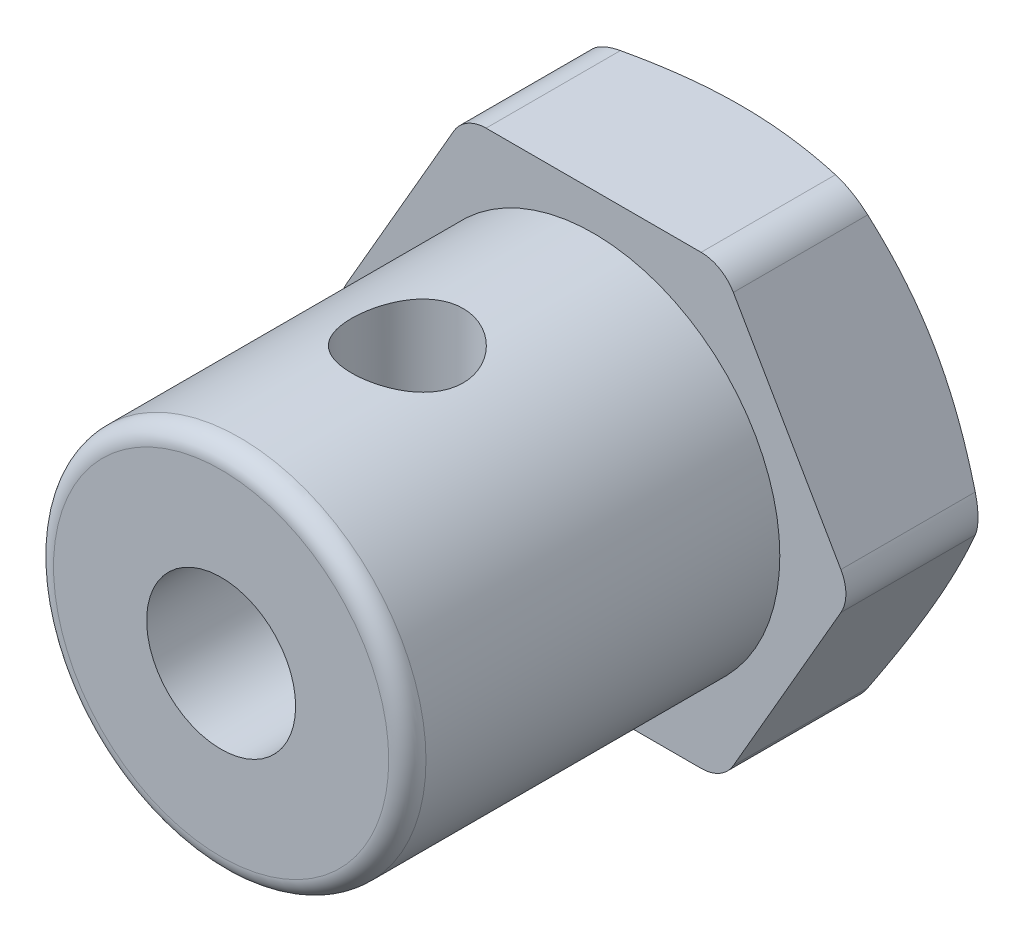
SolidWorks part; units mm, degrees
ref_plane "Front Plane" through (0, 0, 0) normal (0, 0, 1) x (1, 0, 0)
ref_plane "Top Plane" through (0, 0, 0) normal (0, 1, 0) x (1, 0, 0)
ref_plane "Right Plane" through (0, 0, 0) normal (1, 0, 0) x (0, 0, -1)
sketch "Sketch1" plane through (0, 0, 0) normal (0, 0, 1) x (1, 0, 0)
  line L1 (-2.8868, -6) -> (2.8868, -6)
  line L2 (3.7528, -5.5) -> (6.6395, -0.5)
  line L3 (6.6395, 0.5) -> (3.7528, 5.5)
  line L4 (2.8868, 6) -> (-2.8868, 6)
  line L5 (-3.7528, 5.5) -> (-6.6395, 0.5)
  line L6 (-6.6395, -0.5) -> (-3.7528, -5.5)
  circle A0 centre (0, 0) radius 6 construction
  arc A1 (-2.8868, 6) -> (-3.7528, 5.5) centre (-2.8868, 5) ccw
  arc A2 (-6.6395, 0.5) -> (-6.6395, -0.5) centre (-5.7735, 0) ccw
  arc A3 (-2.8868, -6) -> (-3.7528, -5.5) centre (-2.8868, -5) cw
  arc A4 (2.8868, -6) -> (3.7528, -5.5) centre (2.8868, -5) ccw
  arc A5 (6.6395, -0.5) -> (6.6395, 0.5) centre (5.7735, 0) ccw
  arc A6 (3.7528, 5.5) -> (2.8868, 6) centre (2.8868, 5) ccw
  dimension "D1" = 12
  dimension "D2" = 1
extrude "Boss-Extrude1" add sketch "Sketch1" along normal blind 4
sketch "Sketch2" plane through (0, 0, 4) normal (0, 0, 1) x (1, 0, 0)
  circle A0 centre (0, 0) radius 5
  dimension "D1" = 10
extrude "Boss-Extrude2" add sketch "Sketch2" along normal blind 10
sketch "Sketch3" plane through (0, 0, 14) normal (0, 0, 1) x (1, 0, 0)
  circle A0 centre (0, 0) radius 2
  dimension "D1" = 4
extrude "Cut-Extrude1" cut sketch "Sketch3" against normal through all
hole_wizard "Ø3.0mm Dowel Slot5" positions "Sketch10" profile "Sketch9" size "Ø3.0" standard "ANSI Metric" slot yes end condition through all
sketch "Sketch10" plane through (0, 6, 0) normal (0, 1, 0) x (1, 0, 0)
  line L0 (-5, -14) -> (5, -14) construction
  point P0 (0, -9)
  dimension "D1" = 5
sketch "Sketch9" plane through (0, 6, 9) normal (1, 0, 0) x (0, 0, 1)
  line L0 (0, 0) -> (0, 12)
  line L1 (0, 12) -> (1.5, 12)
  line L2 (1.5, 12) -> (1.5, 0)
  line L5 (1.5, 0) -> (0, 0)
  line L11 (0, -6.35) -> (0, 107.95) construction
  dimension "Thru Hole Dia." = 3
  dimension "Thru Hole Depth" = 12
fillet "Fillet1" radius 0.5 1 edges at (5, 0, 14)
sketch "Sketch12" plane through (0, 0, 0) normal (0, 1, 0) x (1, 0, 0)
  line L0 (0, 0) -> (0, -0.5267)
  line L1 (-3.4497, 0.4706) -> (-4.9894, 0.4706)
  line L2 (-4.9894, 0.4706) -> (-6.9681, -0.5535)
  line L3 (-6.9681, -0.5535) -> (-7.3029, -0.5535)
  line L4 (-7.3029, -0.5535) -> (-7.3029, 1.3363)
  line L5 (-7.3029, 1.3363) -> (0, 1.3363)
  line L6 (0, 1.3363) -> (0, 0)
  line L7 (0, -0.5267) -> (-1.6919, -0.5267)
  line L8 (-1.6919, -0.5267) -> (-3.4497, 0.4706)
  line L9 (0, 3.2302) -> (0, -2.0332) construction
revolve "Cut-Revolve1" cut sketch "Sketch12" angle 360 about L9
